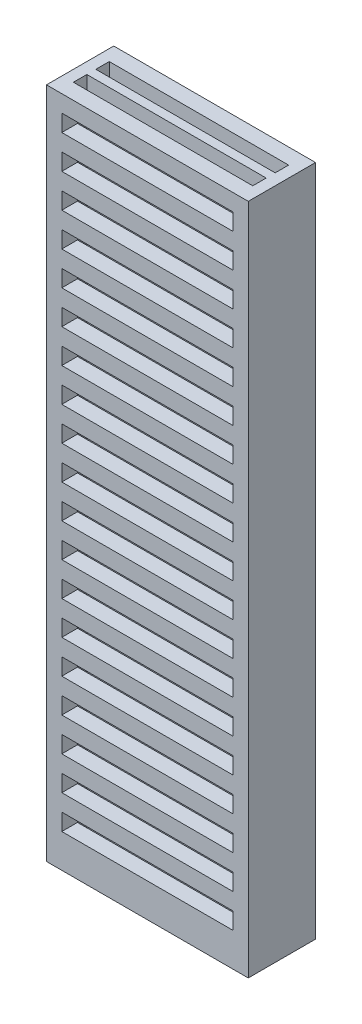
SolidWorks part; units mm, degrees
ref_plane "Front Plane" through (0, 0, 0) normal (0, 0, 1) x (1, 0, 0)
ref_plane "Top Plane" through (0, 0, 0) normal (0, 1, 0) x (1, 0, 0)
ref_plane "Right Plane" through (0, 0, 0) normal (1, 0, 0) x (0, 0, -1)
sketch "Sketch1" plane through (0, 0, 0) normal (0, 1, 0) x (1, 0, 0)
  line L1 (-4.5, -1.5) -> (4.5, -1.5)
  line L2 (-4.5, -1.5) -> (-4.5, 1.5)
  line L3 (-4.5, 1.5) -> (4.5, 1.5)
  line L4 (4.5, -1.5) -> (4.5, 1.5)
  line L5 (-4.5, -1.5) -> (4.5, 1.5) construction
  line L6 (-4.5, 1.5) -> (4.5, -1.5) construction
  point P0 (0, 0)
  dimension "D1" = 9
  dimension "D2" = 3
extrude "Boss-Extrude1" add sketch "Sketch1" along normal mid plane 30
sketch "Sketch2" plane through (0, 15, 0) normal (0, 1, 0) x (1, 0, 0)
  line L1 (-4, 0.2) -> (4, 0.2)
  line L2 (-4, 0.2) -> (-4, 0.8)
  line L3 (-4, 0.8) -> (4, 0.8)
  line L4 (4, 0.2) -> (4, 0.8)
  line L5 (-4, 0.2) -> (4, 0.8) construction
  line L6 (-4, 0.8) -> (4, 0.2) construction
  point P0 (0, 0.5)
  dimension "D1" = 0.6
  dimension "D2" = 8
  dimension "D3" = 0
  dimension "D4" = 0.5
extrude "Cut-Extrude1" cut sketch "Sketch2" against normal through all and the other way through all
mirror "Mirror1" about plane through (0, 0, 0) normal (0, 0, 1) of "Cut-Extrude1"
sketch "Sketch3" plane through (0, 0, 1.5) normal (0, 0, 1) x (1, 0, 0)
  line L0 (0, -1.1) -> (0, 1.1) construction
  line L1 (-3.8171, 13.5) -> (3.8171, 13.5)
  line L2 (-3.8171, 13.5) -> (-3.8171, 14.25)
  line L3 (-3.8171, 14.25) -> (3.8171, 14.25)
  line L4 (3.8171, 13.5) -> (3.8171, 14.25)
  line L5 (-3.8171, 13.5) -> (3.8171, 14.25) construction
  line L6 (-3.8171, 14.25) -> (3.8171, 13.5) construction
  line L7 (-4.5, 15) -> (4.5, 15) construction
  point P0 (0, 13.875)
  dimension "D1" = 0.75
  dimension "D2" = 0.75
extrude "Cut-Extrude2" cut sketch "Sketch3" against normal up to next (0.7 mm away)
pattern_linear "LPattern1" count 19 spacing 1.5 along (0, -1, 0) of "Cut-Extrude2"
mirror "Mirror2" about plane through (0, 0, 0) normal (0, 0, 1) of "LPattern1", "Cut-Extrude2"
